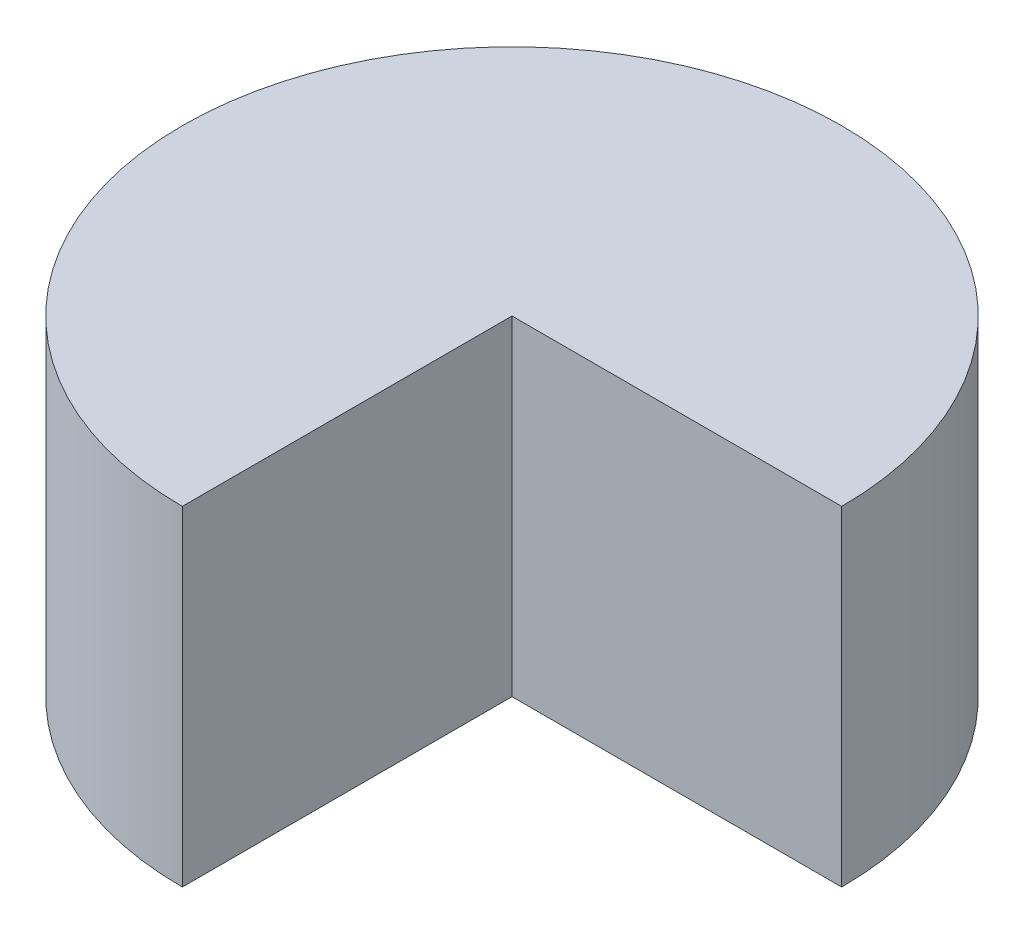
SolidWorks part; units mm, degrees
ref_plane "Front Plane" through (0, 0, 0) normal (0, 0, 1) x (1, 0, 0)
ref_plane "Top Plane" through (0, 0, 0) normal (0, 1, 0) x (1, 0, 0)
ref_plane "Right Plane" through (0, 0, 0) normal (1, 0, 0) x (0, 0, -1)
sketch "Sketch2" plane through (0, 0, 0) normal (0, 1, 0) x (1, 0, 0)
  line L0 (0, 0) -> (80, 0)
  line L2 (0, -80) -> (0, 0)
  arc A1 (0, -80) -> (80, 0) centre (0, 0) cw
  dimension "D1" = 80
  dimension "D2" = 80
extrude "Boss-Extrude1" add sketch "Sketch2" along normal blind 80
shell "Shell1" thickness 5
